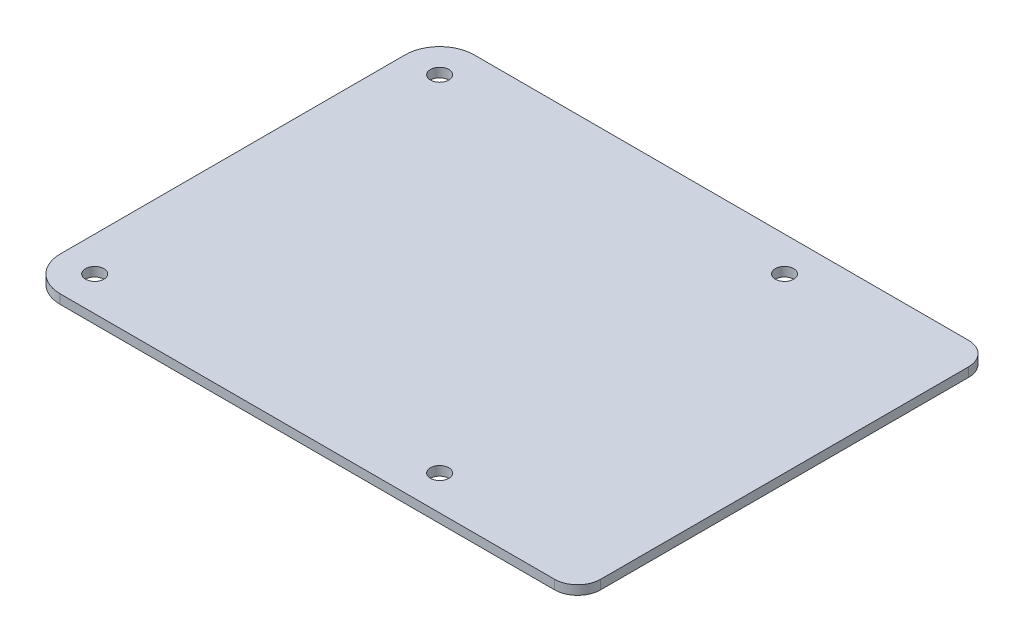
SolidWorks part; units mm, degrees
ref_plane "Front Plane" through (0, 0, 0) normal (0, 0, 1) x (1, 0, 0)
ref_plane "Top Plane" through (0, 0, 0) normal (0, 1, 0) x (1, 0, 0)
ref_plane "Right Plane" through (0, 0, 0) normal (1, 0, 0) x (0, 0, -1)
sketch "Sketch1" plane through (0, 0, 0) normal (0, 1, 0) x (1, 0, 0)
  line L6 (-34, 30) -> (-34, -30)
  line L7 (-28, 36) -> (62, 36)
  line L8 (-28, -36) -> (62, -36)
  line L9 (62, -36) -> (62, 36)
  circle A0 centre (-28, 30) radius 1.6
  circle A1 centre (32, 30) radius 1.6
  circle A2 centre (32, -30) radius 1.6
  circle A3 centre (-28, -30) radius 1.6
  arc A4 (-28, 36) -> (-34, 30) centre (-28, 30) ccw
  arc A5 (-34, -30) -> (-28, -36) centre (-28, -30) ccw
  dimension "D1" = 60
  dimension "D2" = 60
  dimension "D3" = 60
  dimension "D4" = 96
  dimension "D5" = 72
extrude "Boss-Extrude1" add sketch "Sketch1" along normal blind 1.6
fillet "Fillet1" radius 4 2 edges at (62, 0.8, -36) (62, 0.8, 36)
